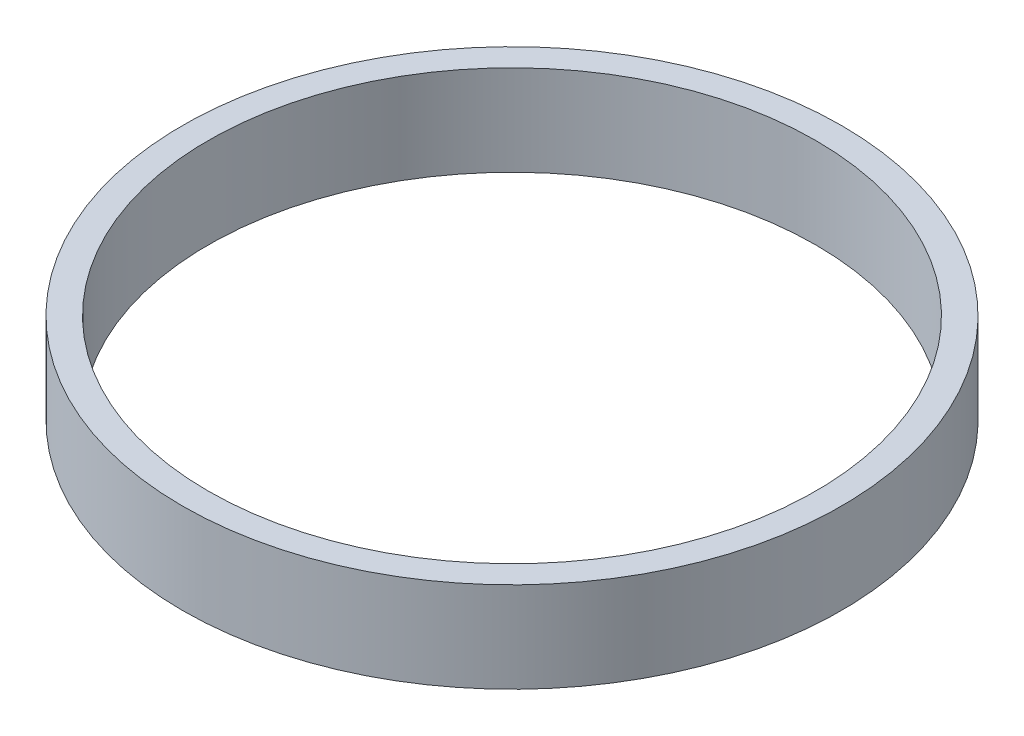
SolidWorks part; units mm, degrees
ref_plane "前视基准面" through (0, 0, 0) normal (0, 0, 1) x (1, 0, 0)
ref_plane "上视基准面" through (0, 0, 0) normal (0, 1, 0) x (1, 0, 0)
ref_plane "右视基准面" through (0, 0, 0) normal (1, 0, 0) x (0, 0, -1)
sketch "草图1" plane through (0, 0, 0) normal (0, 1, 0) x (1, 0, 0)
  circle A0 centre (0, 0) radius 25.5
  circle A1 centre (0, 0) radius 23.5
extrude "凸台-拉伸1" add sketch "草图1" along normal blind 7
